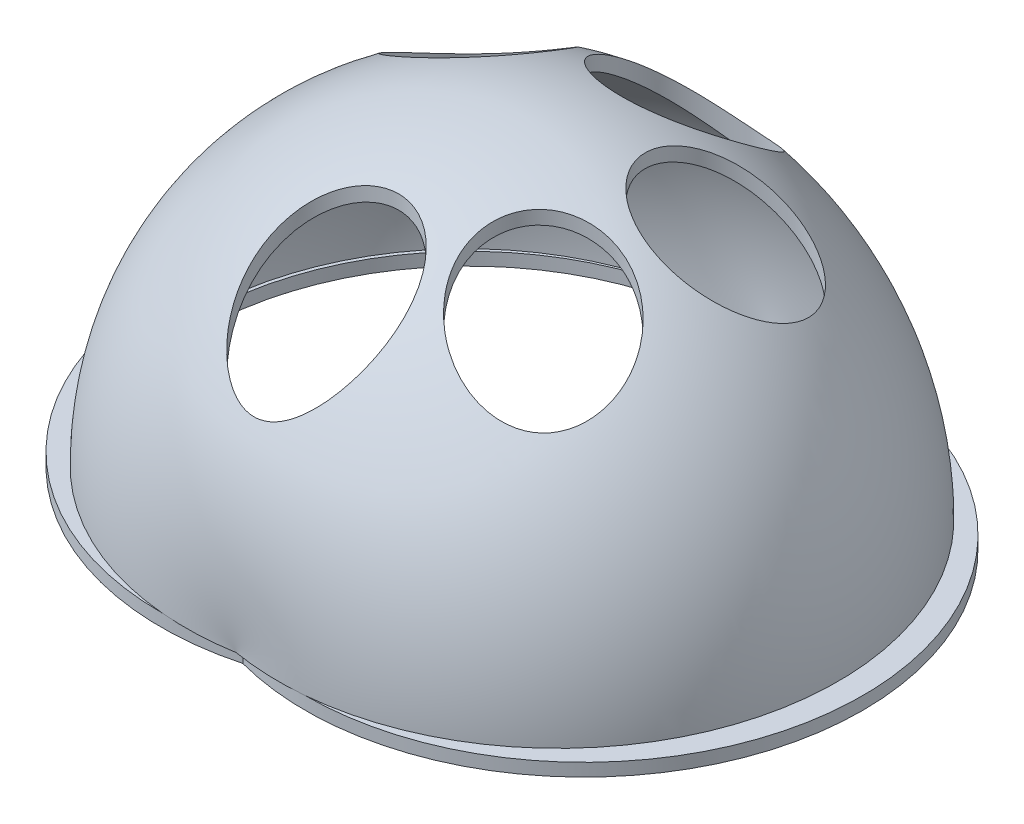
SolidWorks part; units mm, degrees
ref_plane "Front Plane" through (0, 0, 0) normal (0, 0, 1) x (1, 0, 0)
ref_plane "Top Plane" through (0, 0, 0) normal (0, 1, 0) x (1, 0, 0)
ref_plane "Right Plane" through (0, 0, 0) normal (1, 0, 0) x (0, 0, -1)
sketch "Sketch2" plane through (0, 0, 0) normal (0, 1, 0) x (1, 0, 0)
  line L2 (0, 46.5728) -> (0, 41.9511) construction
  line L5 (0, 41.0757) -> (0, -41.8231) construction
  line L6 (0, -41.9511) -> (0, -50.4918) construction
  arc A4 (0, 41.0757) -> (0, -41.8231) centre (-6.3836, -0.3737) ccw
  arc A5 (0, 41.9511) -> (0, -41.9511) centre (-11.2207, 0) ccw
  arc A6 (0, 41.0757) -> (0, -41.8231) centre (6.3836, -0.3737) cw
  arc A7 (0, 41.9511) -> (0, -41.9511) centre (11.2207, 0) cw
extrude "Boss-Extrude1" add sketch "Sketch2" along normal blind 2
sketch "Sketch3" plane through (0, 0, 0) normal (0, 1, 0) x (1, 0, 0)
  circle A0 centre (-20.9927, 15.7767) radius 11
  circle A1 centre (2.3182, 24.5344) radius 11
  circle A2 centre (23.6972, 9.5948) radius 11
  circle A3 centre (20.405, -15.5207) radius 11
  circle A4 centre (-1.8031, -27.1102) radius 11
  point P6 (2.3182, -26.4662)
  point P7 (-20.9927, 15.7767)
  point P8 (0, 0)
  point P11 (0, 0)
sketch "Sketch4" plane through (0, 2, 0) normal (0, 1, 0) x (1, 0, 0)
  line L0 (0, 43) -> (0, 41)
  line L1 (0, -41) -> (0, -43)
  circle A0 centre (0, 0) radius 43 construction
  circle A1 centre (0, 0) radius 41 construction
  arc A2 (0, 43) -> (0, -43) centre (7.2061, 0) cw
  arc A3 (0, 41) -> (0, -41) centre (7.1566, 0) cw
  dimension "D1" = 41.6199
  dimension "D2" = 43.5996
revolve "Revolve1" add sketch "Sketch4" angle 180 about L0
extrude "Cut-Extrude1" cut sketch "Sketch3" along normal blind 62
